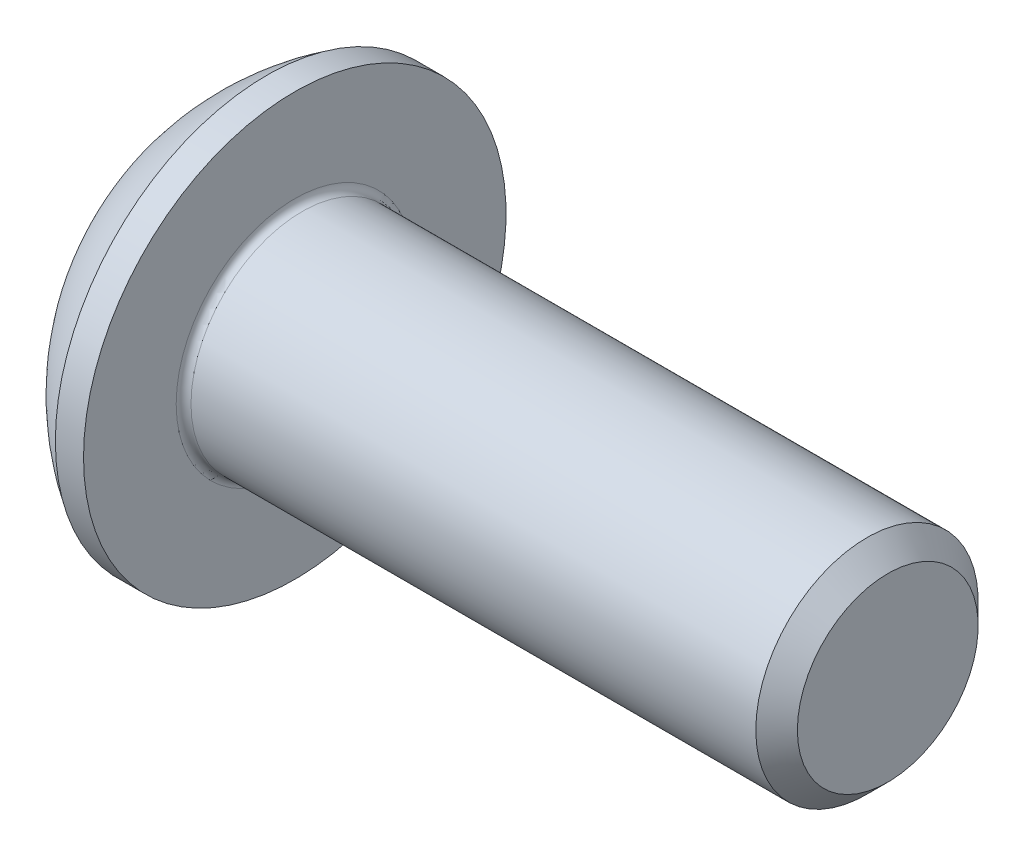
SolidWorks part; units mm, degrees
ref_plane "Plane1" through (0, 0, 0) normal (0, 0, 1) x (1, 0, 0)
ref_plane "Plane2" through (0, 0, 0) normal (0, 1, 0) x (1, 0, 0)
ref_plane "Plane3" through (0, 0, 0) normal (1, 0, 0) x (0, 0, -1)
sketch "BodySke" plane through (0, 0, 0) normal (0, 0, 1) x (1, 0, 0)
  line L0 (9.65, 0) -> (9.65, 1.2195)
  line L1 (9.3695, 1.5) -> (1.65, 1.5)
  line L2 (1.65, 1.5) -> (1.65, 2.85)
  line L3 (1.65, 2.85) -> (1.27, 2.85)
  line L4 (0, 0) -> (101.6, 0) construction
  line L5 (1.65, -2.85) -> (1.27, -2.85) construction
  line L6 (55.6768, -1.5) -> (1.65, -1.5) construction
  line L7 (9.65, 0) -> (0, 0)
  line L8 (0, 1.425) -> (0, -1.425) construction
  line L9 (0, 0) -> (0, 1.425)
  line L10 (9.65, 1.2195) -> (9.3695, 1.5)
  line L11 (9.65, -1.2195) -> (9.3695, -1.5) construction
  line L12 (2.15, 9.525) -> (2.15, -1.5) construction
  line L13 (1.65, 9.525) -> (1.65, -1.5) construction
  arc A1 (0, 1.425) -> (1.27, 2.85) centre (3.0334, 0) cw
  dimension "D1" = 2.85
  dimension "Diameter" = 3
  dimension "Length" = 8
  dimension "Head_dia" = 5.7
  dimension "Head_ht" = 1.65
  dimension "Head_side_ht" = 0.38
  dimension "Minor_dia" = 2.439
  dimension "Body_ch_ang" = 45
  dimension "Advance" = 0.5
  dimension "Thread_nom" = 8
revolve "BaseBody" add sketch "BodySke" angle 360 about L4
cosmetic thread "ThreadCosmetic" [suppressed] parameters "Thread_length"=7, "Thread_minor"=2.439
fillet "Fillet1" radius 0.1 1 edges at (1.65, 0, 1.5)
sketch "Sketch2" plane through (0, 0, 0) normal (0, 0, 1) x (1, 0, 0)
  line L0 (0, 1) -> (1.04, 1)
  line L1 (1.04, 1) -> (1.6174, 0)
  line L3 (1.6174, 0) -> (0, 0)
  line L4 (0, 0) -> (0, 1)
  line L5 (0, -1) -> (1.04, -1) construction
  line L6 (0, 0) -> (47.625, 0) construction
  dimension "D2" = 60
  dimension "PreBroach_depth" = 1.04
  dimension "PreBroach_dia" = 2
revolve "PreBroach" cut sketch "Sketch2" angle 360 about L6
sketch "Sketch3" plane through (0, 0, 0) normal (1, 0, 0) x (0, 0, -1)
  line L0 (-1, -0.5774) -> (-1, 0.5774)
  line L1 (-1, 0.5774) -> (0, 1.1547)
  line L2 (0, 1.1547) -> (1, 0.5774)
  line L3 (1, 0.5774) -> (1, -0.5774)
  line L4 (1, -0.5774) -> (0, -1.1547)
  line L5 (0, -1.1547) -> (-1, -0.5774)
  dimension "D1" = 1
  dimension "D2" = 1
  dimension "D3" = 2
  dimension "Hex_size" = 2
extrude "Hex" cut sketch "Sketch3" along normal blind 1.04
sketch "ThdSchSke" plane through (0, 0, 0) normal (0, 0, 1) x (1, 0, 0)
  line L0 (2.65, -1.2195) -> (2.4536, -1.5)
  line L1 (2.65, -1.2195) -> (2.8464, -1.5)
  line L2 (2.8464, -1.5) -> (2.8464, -1.875)
  line L3 (-3.175, 0) -> (5.1513, 0) construction
  line L5 (2.8464, -1.875) -> (2.4536, -1.875)
  line L6 (2.4536, -1.875) -> (2.4536, -1.5)
  dimension "Thread_minor" = 2.439
  dimension "Diameter" = 3
  dimension "Start" = 2.65
  dimension "SideAngle" = 55
  dimension "VeeAngle" = 70
  dimension "Overcut" = 3.75
revolve "ThreadSchematic" [suppressed] cut sketch "ThdSchSke" angle 360 about L3
pattern_linear "ThdSchPat" [suppressed]
equation "\"D1@BodySke\" = \"Head_dia@BodySke\" * .5"
equation "\"Thread_minor@ThreadCosmetic\" = \"Minor_dia@BodySke\""
equation "\"D1@Sketch3\" = \"Hex_size@Sketch3\" / 2"
equation "\"D2@Sketch3\" = \"D1@Sketch3\""
equation "\"D3@Sketch3\" = \"Hex_size@Sketch3\""
equation "\"Thread_length@ThreadCosmetic\" = ((sgn( (\"Length@BodySke\" - \"Advance@BodySke\" * 2.0) - \"Thread_nom@BodySke\" )-1)*( (\"Length@BodySke\" - \"Advance@BodySke\" * 2.0) - \"Thread_nom@BodySke\" ))/-2+ \"Thread_nom@BodySke\""
equation "\"Thread_minor@ThdSchSke\" = \"Minor_dia@BodySke\""
equation "\"Diameter@ThdSchSke\" = \"Diameter@BodySke\""
equation "\"Overcut@ThdSchSke\" = \"Diameter@BodySke\" * 1.25"
equation "\"Start@ThdSchSke\" = \"Head_ht@BodySke\" + \"Length@BodySke\" - \"Thread_length@ThreadCosmetic\"  '---Non-countersunk---"
equation "\"Num_threads@ThdSchPat\" = int( \"Thread_length@ThreadCosmetic\" / \"Advance@BodySke\" + 0.999 )  + 1"
equation "\"Advance@ThdSchPat\" = \"Thread_length@ThreadCosmetic\" /  (\"Num_threads@ThdSchPat\" - 1) 'relax it"
equation "\"Num_threads@ThdSchPat\" = \"Num_threads@ThdSchPat\" - sgn( \"Num_threads@ThdSchPat\" - 1) '---chamfered tips only---"
